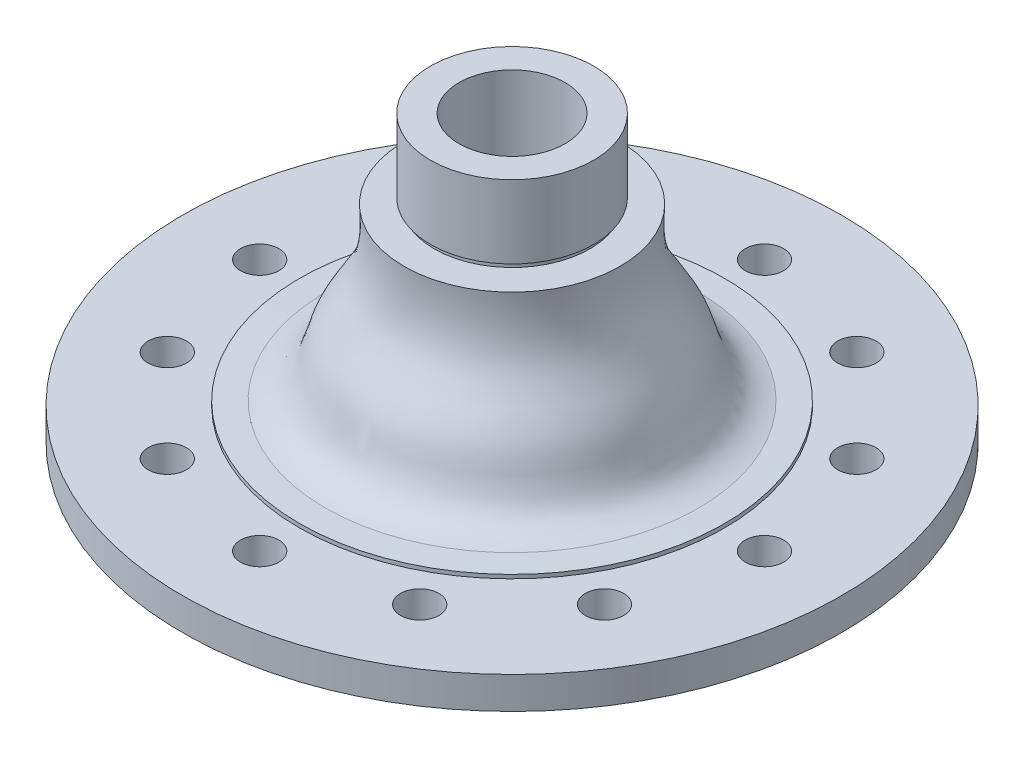
SolidWorks part; units mm, degrees
ref_plane "前视基准面" through (0, 0, 0) normal (0, 0, 1) x (1, 0, 0)
ref_plane "上视基准面" through (0, 0, 0) normal (0, 1, 0) x (1, 0, 0)
ref_plane "右视基准面" through (0, 0, 0) normal (1, 0, 0) x (0, 0, -1)
sketch "草图1" plane through (0, 0, 0) normal (0, 0, 1) x (1, 0, 0)
  line L0 (480.1019, -245.7954) -> (480.1019, -235.2999)
  line L1 (480.1019, -189.0989) -> (480.1019, -199.5944)
  line L2 (570.5144, -106.8394) -> (570.5144, -27.9384)
  line L3 (554.8914, -106.8394) -> (570.5144, -106.8394)
  line L4 (421.1305, -166.2628) -> (451.02, -166.2628)
  line L5 (538.9638, -278.2864) -> (554.8914, -278.2864)
  line L6 (538.9638, -156.6079) -> (554.8914, -156.6079)
  line L7 (479.0172, -166.2494) -> (436.8834, -166.2494)
  line L8 (417.9807, -168.3627) -> (417.9807, -180.6994)
  line L9 (417.9807, -266.5316) -> (417.9807, -254.1949)
  line L10 (479.0172, -164.221) -> (483.3535, -164.221)
  line L11 (554.8914, -156.6079) -> (554.8914, -106.8394)
  line L12 (554.8914, -67.8359) -> (554.8914, -43.8433)
  line L13 (628.5144, -106.8394) -> (628.5144, -27.9384)
  line L14 (644.1375, -106.8394) -> (628.5144, -106.8394)
  line L15 (660.0651, -156.6079) -> (644.1375, -156.6079)
  line L16 (644.1375, -156.6079) -> (644.1375, -106.8394)
  line L17 (660.0651, -278.2864) -> (644.1375, -278.2864)
  line L18 (644.1367, -27.9384) -> (644.1367, -67.8359)
  line L19 (554.8922, -27.9384) -> (554.8922, -66.786)
  line L20 (540.4804, -70.9857) -> (556.9913, -70.9857)
  line L21 (556.9913, -70.9857) -> (556.9913, -67.8359)
  line L22 (556.9913, -67.8359) -> (554.8914, -67.8359)
  line L23 (628.5144, -27.9384) -> (554.8922, -27.9384)
  line L24 (658.5485, -70.9857) -> (642.0376, -70.9857)
  line L25 (642.0376, -67.8359) -> (644.27, -67.8359)
  line L26 (642.0376, -70.9857) -> (642.0376, -67.8359)
  line L27 (644.1375, -328.0549) -> (628.5144, -328.0549)
  line L28 (554.8914, -67.8359) -> (554.7589, -67.8359)
  line L29 (715.6754, -164.221) -> (715.6754, -166.3209)
  line L30 (715.6754, -164.221) -> (701.5796, -163.8762)
  line L31 (483.3535, -164.221) -> (497.4492, -163.8762)
  line L32 (554.8914, -406.9559) -> (573.2661, -406.9559)
  line L33 (554.8914, -367.0584) -> (554.8914, -406.9559)
  line L34 (644.1367, -402.7562) -> (644.1367, -368.1083)
  line L35 (554.8922, -402.7562) -> (554.8922, -368.1083)
  line L36 (648.3364, -363.9086) -> (658.5485, -363.9086)
  line L37 (540.4804, -363.9086) -> (554.8914, -363.9086)
  line L38 (554.8914, -363.9086) -> (556.9913, -363.9086)
  line L39 (556.9913, -363.9086) -> (556.9913, -367.0584)
  line L40 (556.9913, -367.0584) -> (554.7589, -367.0584)
  line L41 (644.1367, -406.9559) -> (625.7628, -406.9559)
  line L42 (573.2661, -406.9559) -> (554.8914, -406.9559)
  line L43 (648.3364, -363.9086) -> (642.0376, -363.9086)
  line L44 (642.0376, -367.0584) -> (644.2621, -367.0584)
  line L45 (642.0376, -363.9086) -> (642.0376, -367.0584)
  line L46 (644.1375, -278.2864) -> (644.1375, -328.0549)
  line L47 (480.1019, -199.5944) -> (517.9771, -199.5944)
  line L48 (483.2517, -235.2999) -> (509.5902, -235.2999)
  line L49 (718.927, -199.5944) -> (681.1417, -199.5944)
  line L50 (718.927, -235.2999) -> (681.1417, -235.2999)
  line L51 (781.0482, -168.3627) -> (781.0482, -180.6994)
  line L52 (480.1019, -235.2999) -> (517.9758, -235.2999)
  line L53 (718.927, -199.5944) -> (681.053, -199.5944)
  line L54 (681.0398, -235.2999) -> (718.927, -235.2999)
  line L55 (718.927, -189.0989) -> (718.927, -199.5944)
  line L56 (718.927, -245.7954) -> (718.927, -235.2999)
  line L57 (660.0651, -156.6471) -> (660.0651, -156.6079)
  line L58 (456.4437, -166.2628) -> (420.0806, -166.2628)
  line L59 (479.0172, -164.221) -> (479.0172, -166.2494)
  line L60 (473.7676, -166.2494) -> (472.8541, -166.2494)
  line L61 (417.9807, -266.5316) -> (417.9807, -254.1949)
  line L62 (456.4437, -268.6315) -> (420.0806, -268.6315)
  line L63 (479.0172, -268.6315) -> (420.0806, -268.6315)
  line L64 (483.3535, -270.6733) -> (497.4492, -271.0181)
  line L65 (479.0172, -270.6733) -> (479.0172, -268.6315)
  line L66 (479.0172, -270.6733) -> (483.3535, -270.6733)
  line L67 (421.1305, -183.8492) -> (474.8522, -183.8492)
  line L68 (421.1305, -251.0451) -> (474.8522, -251.0451)
  line L69 (715.6754, -270.6733) -> (701.5796, -271.0181)
  line L70 (720.0116, -270.6733) -> (720.0116, -268.6315)
  line L71 (781.0482, -266.5316) -> (781.0482, -254.1949)
  line L72 (720.0116, -268.6315) -> (778.9483, -268.6315)
  line L73 (720.0116, -270.6733) -> (715.6754, -270.6733)
  line L74 (777.8983, -183.8492) -> (724.1766, -183.8492)
  line L75 (777.8983, -251.0451) -> (724.1766, -251.0451)
  line L76 (554.8914, -328.0549) -> (554.946, -328.0549)
  line L77 (554.946, -328.0549) -> (570.5144, -328.0549)
  line L78 (554.8914, -278.2864) -> (554.8914, -328.0549)
  line L79 (644.1367, -367.0584) -> (644.1367, -406.9559)
  line L80 (628.5144, -27.9384) -> (644.1367, -27.9384)
  line L81 (573.2661, -406.9559) -> (625.7628, -406.9559)
  line L82 (443.3195, -166.2494) -> (443.3195, -183.8492)
  line L83 (443.3195, -251.0451) -> (443.3195, -268.6315)
  line L84 (466.418, -166.2494) -> (466.418, -183.8492)
  line L85 (466.418, -251.0451) -> (466.418, -268.6315)
  line L86 (570.5144, -328.0549) -> (570.5144, -406.9559)
  line L87 (628.5144, -328.0549) -> (628.5144, -406.9559)
  line L88 (715.6754, -166.3209) -> (778.9483, -166.3209)
  line L89 (755.7094, -166.2494) -> (755.7094, -183.8492)
  line L90 (754.6595, -166.2494) -> (754.6595, -166.3209)
  line L91 (733.6608, -166.2494) -> (733.6608, -166.3209)
  line L92 (732.6108, -166.2494) -> (732.6108, -183.8492)
  line L93 (755.7094, -251.0451) -> (755.7094, -268.6315)
  line L94 (732.6108, -251.0451) -> (732.6108, -268.6315)
  arc A0 (525.3047, -175.8868) -> (517.9771, -199.5944) centre (584.1341, -207.0561) ccw
  arc A1 (417.9807, -180.6994) -> (421.1305, -183.8492) centre (421.1305, -180.6994) ccw
  arc A2 (420.0806, -166.2628) -> (417.9807, -168.3627) centre (420.0806, -168.3627) ccw
  arc A3 (421.1305, -251.0451) -> (417.9807, -254.1949) centre (421.1305, -254.1949) ccw
  arc A4 (681.053, -199.5944) -> (673.7242, -175.8868) centre (614.8603, -207.0702) ccw
  arc A5 (517.9758, -235.2999) -> (525.3047, -259.0076) centre (584.1686, -227.8242) ccw
  arc A6 (673.7242, -259.0076) -> (681.053, -235.2999) centre (614.8603, -227.8242) ccw
  arc A7 (781.0482, -168.3627) -> (778.9483, -166.2628) centre (778.9483, -168.3627) ccw
  arc A8 (777.8983, -183.8492) -> (781.0482, -180.6994) centre (777.8983, -180.6994) ccw
  arc A9 (480.1019, -189.0989) -> (474.8522, -183.8492) centre (474.8522, -189.0989) ccw
  arc A10 (474.8522, -251.0451) -> (480.1019, -245.7954) centre (474.8522, -245.7954) ccw
  arc A11 (724.1766, -183.8492) -> (718.927, -189.0989) centre (724.1766, -189.0989) ccw
  arc A12 (718.927, -245.7954) -> (724.1766, -251.0451) centre (724.1766, -245.7954) ccw
  arc A13 (417.9807, -266.5316) -> (420.0806, -268.6315) centre (420.0806, -266.5316) ccw
  arc A14 (421.1305, -251.0451) -> (417.9807, -254.1949) centre (421.1305, -254.1949) ccw
  arc A15 (781.0482, -254.1949) -> (777.8983, -251.0451) centre (777.8983, -254.1949) ccw
  arc A16 (778.9483, -268.6315) -> (781.0482, -266.5316) centre (778.9483, -266.5316) ccw
  spline S0 degree 3 poles (701.5796, -163.8762) (696.837, -162.8738) (682.4852, -157.6762) (679.9458, -129.4237) (658.4817, -105.8546) (657.727, -82.1258) (658.5485, -70.9857) knots 0 0 0 0 1057.430308 2997.111063 5402.743205 7834.148235 7834.148235 7834.148235 7834.148235 weights 1 1 1 1 1 1 1
  spline S1 degree 3 poles (497.4492, -163.8762) (502.1919, -162.8738) (516.5437, -157.6762) (519.083, -129.4237) (540.5472, -105.8546) (541.3019, -82.1258) (540.4804, -70.9857) knots 0 0 0 0 836.310079 2370.382399 4272.970581 6195.942259 6195.942259 6195.942259 6195.942259 weights 1 1 1 1 1 1 1
  spline S2 degree 3 poles (538.9638, -156.6079) (535.9309, -156.9888) (531.5182, -158.6747) (524.9801, -164.8379) (524.3832, -171.6216) (525.3047, -175.8868) knots 0 0 0 0 1737.139201 2548.792041 5028.650795 5028.650795 5028.650795 5028.650795 weights 1 1 1 1 1 1
  spline S3 degree 3 poles (660.0651, -156.6079) (663.098, -156.9888) (667.5107, -158.6747) (674.0488, -164.8379) (674.6457, -171.6216) (673.7242, -175.8868) knots 0 0 0 0 2126.07148 3119.447228 6154.52753 6154.52753 6154.52753 6154.52753 weights 1 1 1 1 1 1
  spline S4 degree 3 poles (538.9638, -278.2864) (535.9309, -277.9055) (531.5182, -276.2196) (524.9801, -270.0564) (524.3832, -263.2727) (525.3047, -259.0076) knots 0 0 0 0 1950.629452 2862.032483 5646.659944 5646.659944 5646.659944 5646.659944 weights 1 1 1 1 1 1
  spline S5 degree 3 poles (660.0651, -278.2864) (663.098, -277.9055) (667.5107, -276.2196) (674.0488, -270.0564) (674.6457, -263.2727) (673.7242, -259.0076) knots 0 0 0 0 2328.664854 3416.699389 6740.992526 6740.992526 6740.992526 6740.992526 weights 1 1 1 1 1 1
  spline S6 degree 3 poles (497.4492, -271.0181) (502.1919, -272.0205) (516.5437, -277.2181) (519.083, -305.4706) (540.5472, -329.0397) (541.3019, -352.7686) (540.4804, -363.9086) knots 0 0 0 0 1000.918373 2836.937343 5114.005999 7415.470169 7415.470169 7415.470169 7415.470169 weights 1 1 1 1 1 1 1
  spline S7 degree 3 poles (701.5796, -271.0181) (696.837, -272.0205) (682.4852, -277.2181) (679.9458, -305.4706) (658.4817, -329.0397) (657.727, -352.7686) (658.5485, -363.9086) knots 0 0 0 0 1212.145887 3435.626744 6193.233637 8980.38432 8980.38432 8980.38432 8980.38432 weights 1 1 1 1 1 1 1
  dimension "D1" = 58
sketch "草图2" plane through (0, 0, 0) normal (0, 0, 1) x (1, 0, 0)
  line L0 (628.5144, -67.3889) -> (570.5144, -67.3889)
  line L1 (628.5144, -106.8394) -> (628.5144, -27.9384) construction
  line L2 (570.5144, -106.8394) -> (570.5144, -27.9384) construction
  line L3 (599.5144, -67.3889) -> (599.5144, -145.6422)
  line L4 (628.5144, -106.8394) -> (628.5144, -27.9384)
  line L5 (658.5485, -70.9857) -> (642.0376, -70.9857) construction
  line L6 (658.5485, -70.9857) -> (642.0376, -70.9857)
  line L7 (421.1305, -166.2628) -> (451.02, -166.2628) construction
  line L8 (554.8914, -106.8394) -> (570.5144, -106.8394) construction
  line L9 (554.8914, -156.6079) -> (554.8914, -106.8394) construction
  line L10 (538.9638, -156.6079) -> (554.8914, -156.6079) construction
  line L11 (570.5144, -328.0549) -> (570.5144, -406.9559) construction
  line L12 (554.946, -328.0549) -> (570.5144, -328.0549) construction
  line L13 (554.8914, -328.0549) -> (554.946, -328.0549) construction
  line L14 (554.8914, -278.2864) -> (554.8914, -328.0549) construction
  line L15 (538.9638, -278.2864) -> (554.8914, -278.2864) construction
  line L16 (480.1019, -235.2999) -> (517.9758, -235.2999) construction
  line L17 (480.1019, -245.7954) -> (480.1019, -235.2999) construction
  line L18 (421.1305, -251.0451) -> (474.8522, -251.0451) construction
  line L19 (417.9807, -266.5316) -> (417.9807, -254.1949) construction
  line L20 (417.9807, -266.5316) -> (417.9807, -254.1949) construction
  line L21 (556.9913, -67.8359) -> (554.8914, -67.8359) construction
  line L22 (556.9913, -70.9857) -> (556.9913, -67.8359) construction
  line L23 (540.4804, -70.9857) -> (556.9913, -70.9857) construction
  line L24 (483.3535, -164.221) -> (497.4492, -163.8762) construction
  line L25 (479.0172, -164.221) -> (483.3535, -164.221) construction
  line L26 (479.0172, -164.221) -> (479.0172, -166.2494) construction
  line L27 (479.0172, -166.2494) -> (436.8834, -166.2494) construction
  line L28 (644.1367, -27.9384) -> (644.1367, -67.8359) construction
  line L29 (628.5144, -27.9384) -> (644.1367, -27.9384) construction
  line L30 (644.1375, -106.8394) -> (628.5144, -106.8394) construction
  line L31 (644.1375, -156.6079) -> (644.1375, -106.8394) construction
  line L32 (660.0651, -156.6079) -> (644.1375, -156.6079) construction
  line L33 (660.0651, -156.6471) -> (660.0651, -156.6079) construction
  line L34 (718.927, -199.5944) -> (681.053, -199.5944) construction
  line L35 (554.8922, -27.9384) -> (554.8922, -66.786) construction
  line L36 (628.5144, -27.9384) -> (554.8922, -27.9384) construction
  line L37 (554.8914, -67.8359) -> (554.8914, -43.8433) construction
  line L38 (554.8914, -67.8359) -> (554.7589, -67.8359) construction
  line L39 (554.8914, -406.9559) -> (573.2661, -406.9559) construction
  line L40 (554.8914, -367.0584) -> (554.8914, -406.9559) construction
  line L41 (573.2661, -406.9559) -> (554.8914, -406.9559) construction
  line L42 (642.0376, -67.8359) -> (644.27, -67.8359) construction
  line L43 (642.0376, -70.9857) -> (642.0376, -67.8359) construction
  line L44 (715.6754, -164.221) -> (701.5796, -163.8762) construction
  line L45 (715.6754, -164.221) -> (715.6754, -166.3209) construction
  line L46 (715.6754, -166.3209) -> (778.9483, -166.3209) construction
  line L47 (479.0172, -268.6315) -> (420.0806, -268.6315) construction
  line L48 (479.0172, -270.6733) -> (479.0172, -268.6315) construction
  line L49 (479.0172, -270.6733) -> (483.3535, -270.6733) construction
  line L50 (483.3535, -270.6733) -> (497.4492, -271.0181) construction
  line L51 (540.4804, -363.9086) -> (554.8914, -363.9086) construction
  line L52 (554.8914, -363.9086) -> (556.9913, -363.9086) construction
  line L53 (556.9913, -363.9086) -> (556.9913, -367.0584) construction
  line L54 (556.9913, -367.0584) -> (554.7589, -367.0584) construction
  line L55 (554.8922, -402.7562) -> (554.8922, -368.1083) construction
  line L56 (644.1367, -402.7562) -> (644.1367, -368.1083) construction
  line L57 (573.2661, -406.9559) -> (625.7628, -406.9559) construction
  line L58 (644.1367, -406.9559) -> (625.7628, -406.9559) construction
  line L59 (644.1367, -367.0584) -> (644.1367, -406.9559) construction
  line L60 (660.0651, -278.2864) -> (644.1375, -278.2864) construction
  line L61 (644.1375, -278.2864) -> (644.1375, -328.0549) construction
  line L62 (644.1375, -328.0549) -> (628.5144, -328.0549) construction
  line L63 (628.5144, -328.0549) -> (628.5144, -406.9559) construction
  line L64 (718.927, -235.2999) -> (681.1417, -235.2999) construction
  line L65 (681.0398, -235.2999) -> (718.927, -235.2999) construction
  line L66 (642.0376, -367.0584) -> (644.2621, -367.0584) construction
  line L67 (642.0376, -363.9086) -> (642.0376, -367.0584) construction
  line L68 (648.3364, -363.9086) -> (642.0376, -363.9086) construction
  line L69 (648.3364, -363.9086) -> (658.5485, -363.9086) construction
  line L70 (715.6754, -270.6733) -> (701.5796, -271.0181) construction
  line L71 (720.0116, -270.6733) -> (715.6754, -270.6733) construction
  line L72 (720.0116, -270.6733) -> (720.0116, -268.6315) construction
  line L73 (720.0116, -268.6315) -> (778.9483, -268.6315) construction
  line L74 (781.0482, -266.5316) -> (781.0482, -254.1949) construction
  line L75 (777.8983, -251.0451) -> (724.1766, -251.0451) construction
  line L76 (718.927, -245.7954) -> (718.927, -235.2999) construction
  line L77 (718.927, -199.5944) -> (681.1417, -199.5944) construction
  line L78 (781.0482, -168.3627) -> (781.0482, -180.6994) construction
  line L79 (777.8983, -183.8492) -> (724.1766, -183.8492) construction
  line L80 (718.927, -189.0989) -> (718.927, -199.5944) construction
  line L81 (483.2517, -235.2999) -> (509.5902, -235.2999) construction
  line L82 (456.4437, -166.2628) -> (420.0806, -166.2628) construction
  line L83 (417.9807, -168.3627) -> (417.9807, -180.6994) construction
  line L84 (421.1305, -183.8492) -> (474.8522, -183.8492) construction
  line L85 (480.1019, -189.0989) -> (480.1019, -199.5944) construction
  line L86 (480.1019, -199.5944) -> (517.9771, -199.5944) construction
  line L87 (456.4437, -268.6315) -> (420.0806, -268.6315) construction
  line L88 (473.7676, -166.2494) -> (472.8541, -166.2494) construction
  line L89 (466.418, -251.0451) -> (466.418, -268.6315) construction
  line L90 (466.418, -166.2494) -> (466.418, -183.8492) construction
  line L91 (443.3195, -251.0451) -> (443.3195, -268.6315) construction
  line L92 (443.3195, -166.2494) -> (443.3195, -183.8492) construction
  line L93 (732.6108, -251.0451) -> (732.6108, -268.6315) construction
  line L94 (755.7094, -251.0451) -> (755.7094, -268.6315) construction
  line L95 (732.6108, -166.2494) -> (732.6108, -183.8492) construction
  line L96 (733.6608, -166.2494) -> (733.6608, -166.3209) construction
  line L97 (754.6595, -166.2494) -> (754.6595, -166.3209) construction
  line L98 (755.7094, -166.2494) -> (755.7094, -183.8492) construction
  line L99 (421.1305, -166.2628) -> (451.02, -166.2628)
  line L100 (570.5144, -106.8394) -> (570.5144, -27.9384)
  line L101 (554.8914, -106.8394) -> (570.5144, -106.8394)
  line L102 (554.8914, -156.6079) -> (554.8914, -106.8394)
  line L103 (538.9638, -156.6079) -> (554.8914, -156.6079)
  line L104 (570.5144, -328.0549) -> (570.5144, -406.9559)
  line L105 (554.946, -328.0549) -> (570.5144, -328.0549)
  line L106 (554.8914, -328.0549) -> (554.946, -328.0549)
  line L107 (554.8914, -278.2864) -> (554.8914, -328.0549)
  line L108 (538.9638, -278.2864) -> (554.8914, -278.2864)
  line L109 (480.1019, -235.2999) -> (517.9758, -235.2999)
  line L110 (480.1019, -245.7954) -> (480.1019, -235.2999)
  line L111 (421.1305, -251.0451) -> (474.8522, -251.0451)
  line L112 (417.9807, -266.5316) -> (417.9807, -254.1949)
  line L113 (417.9807, -266.5316) -> (417.9807, -254.1949)
  line L114 (556.9913, -67.8359) -> (554.8914, -67.8359)
  line L115 (556.9913, -70.9857) -> (556.9913, -67.8359)
  line L116 (540.4804, -70.9857) -> (556.9913, -70.9857)
  line L117 (483.3535, -164.221) -> (497.4492, -163.8762)
  line L118 (479.0172, -164.221) -> (483.3535, -164.221)
  line L119 (479.0172, -164.221) -> (479.0172, -166.2494)
  line L120 (479.0172, -166.2494) -> (436.8834, -166.2494)
  line L121 (644.1367, -27.9384) -> (644.1367, -67.8359)
  line L122 (628.5144, -27.9384) -> (644.1367, -27.9384)
  line L123 (628.5144, -106.8394) -> (628.5144, -27.9384)
  line L124 (644.1375, -106.8394) -> (628.5144, -106.8394)
  line L125 (644.1375, -156.6079) -> (644.1375, -106.8394)
  line L126 (660.0651, -156.6079) -> (644.1375, -156.6079)
  line L127 (660.0651, -156.6471) -> (660.0651, -156.6079)
  line L128 (718.927, -199.5944) -> (681.053, -199.5944)
  line L129 (554.8922, -27.9384) -> (554.8922, -66.786)
  line L130 (628.5144, -27.9384) -> (554.8922, -27.9384)
  line L131 (554.8914, -67.8359) -> (554.8914, -43.8433)
  line L132 (554.8914, -67.8359) -> (554.7589, -67.8359)
  line L133 (554.8914, -406.9559) -> (573.2661, -406.9559)
  line L134 (554.8914, -367.0584) -> (554.8914, -406.9559)
  line L135 (573.2661, -406.9559) -> (554.8914, -406.9559)
  line L136 (642.0376, -67.8359) -> (644.27, -67.8359)
  line L137 (642.0376, -70.9857) -> (642.0376, -67.8359)
  line L138 (658.5485, -70.9857) -> (642.0376, -70.9857)
  line L139 (715.6754, -164.221) -> (701.5796, -163.8762)
  line L140 (715.6754, -164.221) -> (715.6754, -166.3209)
  line L141 (715.6754, -166.3209) -> (778.9483, -166.3209)
  line L142 (479.0172, -268.6315) -> (420.0806, -268.6315)
  line L143 (479.0172, -270.6733) -> (479.0172, -268.6315)
  line L144 (479.0172, -270.6733) -> (483.3535, -270.6733)
  line L145 (483.3535, -270.6733) -> (497.4492, -271.0181)
  line L146 (540.4804, -363.9086) -> (554.8914, -363.9086)
  line L147 (554.8914, -363.9086) -> (556.9913, -363.9086)
  line L148 (556.9913, -363.9086) -> (556.9913, -367.0584)
  line L149 (556.9913, -367.0584) -> (554.7589, -367.0584)
  line L150 (554.8922, -402.7562) -> (554.8922, -368.1083)
  line L151 (644.1367, -402.7562) -> (644.1367, -368.1083)
  line L152 (573.2661, -406.9559) -> (625.7628, -406.9559)
  line L153 (644.1367, -406.9559) -> (625.7628, -406.9559)
  line L154 (644.1367, -367.0584) -> (644.1367, -406.9559)
  line L155 (660.0651, -278.2864) -> (644.1375, -278.2864)
  line L156 (644.1375, -278.2864) -> (644.1375, -328.0549)
  line L157 (644.1375, -328.0549) -> (628.5144, -328.0549)
  line L158 (628.5144, -328.0549) -> (628.5144, -406.9559)
  line L159 (718.927, -235.2999) -> (681.1417, -235.2999)
  line L160 (681.0398, -235.2999) -> (718.927, -235.2999)
  line L161 (642.0376, -367.0584) -> (644.2621, -367.0584)
  line L162 (642.0376, -363.9086) -> (642.0376, -367.0584)
  line L163 (648.3364, -363.9086) -> (642.0376, -363.9086)
  line L164 (648.3364, -363.9086) -> (658.5485, -363.9086)
  line L165 (715.6754, -270.6733) -> (701.5796, -271.0181)
  line L166 (720.0116, -270.6733) -> (715.6754, -270.6733)
  line L167 (720.0116, -270.6733) -> (720.0116, -268.6315)
  line L168 (720.0116, -268.6315) -> (778.9483, -268.6315)
  line L169 (781.0482, -266.5316) -> (781.0482, -254.1949)
  line L170 (777.8983, -251.0451) -> (724.1766, -251.0451)
  line L171 (718.927, -245.7954) -> (718.927, -235.2999)
  line L172 (718.927, -199.5944) -> (681.1417, -199.5944)
  line L173 (781.0482, -168.3627) -> (781.0482, -180.6994)
  line L174 (777.8983, -183.8492) -> (724.1766, -183.8492)
  line L175 (718.927, -189.0989) -> (718.927, -199.5944)
  line L176 (483.2517, -235.2999) -> (509.5902, -235.2999)
  line L177 (456.4437, -166.2628) -> (420.0806, -166.2628)
  line L178 (417.9807, -168.3627) -> (417.9807, -180.6994)
  line L179 (421.1305, -183.8492) -> (474.8522, -183.8492)
  line L180 (480.1019, -189.0989) -> (480.1019, -199.5944)
  line L181 (480.1019, -199.5944) -> (517.9771, -199.5944)
  line L182 (456.4437, -268.6315) -> (420.0806, -268.6315)
  line L183 (473.7676, -166.2494) -> (472.8541, -166.2494)
  line L184 (466.418, -251.0451) -> (466.418, -268.6315)
  line L185 (466.418, -166.2494) -> (466.418, -183.8492)
  line L186 (443.3195, -251.0451) -> (443.3195, -268.6315)
  line L187 (443.3195, -166.2494) -> (443.3195, -183.8492)
  line L188 (732.6108, -251.0451) -> (732.6108, -268.6315)
  line L189 (755.7094, -251.0451) -> (755.7094, -268.6315)
  line L190 (732.6108, -166.2494) -> (732.6108, -183.8492)
  line L191 (733.6608, -166.2494) -> (733.6608, -166.3209)
  line L193 (755.7094, -166.2494) -> (755.7094, -183.8492)
  line L194 (421.1305, -166.2628) -> (451.02, -166.2628)
  line L195 (570.5144, -106.8394) -> (570.5144, -27.9384)
  line L196 (554.8914, -106.8394) -> (570.5144, -106.8394)
  line L197 (554.8914, -156.6079) -> (554.8914, -106.8394)
  line L198 (538.9638, -156.6079) -> (554.8914, -156.6079)
  line L199 (570.5144, -328.0549) -> (570.5144, -406.9559)
  line L200 (554.946, -328.0549) -> (570.5144, -328.0549)
  line L201 (554.8914, -328.0549) -> (554.946, -328.0549)
  line L202 (554.8914, -278.2864) -> (554.8914, -328.0549)
  line L203 (538.9638, -278.2864) -> (554.8914, -278.2864)
  line L204 (480.1019, -235.2999) -> (517.9758, -235.2999)
  line L205 (480.1019, -245.7954) -> (480.1019, -235.2999)
  line L206 (421.1305, -251.0451) -> (474.8522, -251.0451)
  line L207 (417.9807, -266.5316) -> (417.9807, -254.1949)
  line L208 (417.9807, -266.5316) -> (417.9807, -254.1949)
  line L209 (556.9913, -67.8359) -> (554.8914, -67.8359)
  line L210 (556.9913, -70.9857) -> (556.9913, -67.8359)
  line L211 (540.4804, -70.9857) -> (556.9913, -70.9857)
  line L212 (483.3535, -164.221) -> (497.4492, -163.8762)
  line L213 (479.0172, -164.221) -> (483.3535, -164.221)
  line L214 (479.0172, -164.221) -> (479.0172, -166.2494)
  line L215 (479.0172, -166.2494) -> (436.8834, -166.2494)
  line L216 (644.1367, -27.9384) -> (644.1367, -67.8359)
  line L217 (628.5144, -27.9384) -> (644.1367, -27.9384)
  line L218 (628.5144, -106.8394) -> (628.5144, -27.9384)
  line L219 (644.1375, -106.8394) -> (628.5144, -106.8394)
  line L220 (644.1375, -156.6079) -> (644.1375, -106.8394)
  line L221 (660.0651, -156.6079) -> (644.1375, -156.6079)
  line L222 (660.0651, -156.6471) -> (660.0651, -156.6079)
  line L223 (718.927, -199.5944) -> (681.053, -199.5944)
  line L224 (554.8922, -27.9384) -> (554.8922, -66.786)
  line L225 (628.5144, -27.9384) -> (554.8922, -27.9384)
  line L226 (554.8914, -67.8359) -> (554.8914, -43.8433)
  line L227 (554.8914, -67.8359) -> (554.7589, -67.8359)
  line L228 (554.8914, -406.9559) -> (573.2661, -406.9559)
  line L229 (554.8914, -367.0584) -> (554.8914, -406.9559)
  line L230 (573.2661, -406.9559) -> (554.8914, -406.9559)
  line L231 (642.0376, -67.8359) -> (644.27, -67.8359)
  line L232 (642.0376, -70.9857) -> (642.0376, -67.8359)
  line L233 (658.5485, -70.9857) -> (642.0376, -70.9857)
  line L234 (715.6754, -164.221) -> (701.5796, -163.8762)
  line L235 (715.6754, -164.221) -> (715.6754, -166.3209)
  line L236 (715.6754, -166.3209) -> (778.9483, -166.3209)
  line L237 (479.0172, -268.6315) -> (420.0806, -268.6315)
  line L238 (479.0172, -270.6733) -> (479.0172, -268.6315)
  line L239 (479.0172, -270.6733) -> (483.3535, -270.6733)
  line L240 (483.3535, -270.6733) -> (497.4492, -271.0181)
  line L241 (540.4804, -363.9086) -> (554.8914, -363.9086)
  line L242 (554.8914, -363.9086) -> (556.9913, -363.9086)
  line L243 (556.9913, -363.9086) -> (556.9913, -367.0584)
  line L244 (556.9913, -367.0584) -> (554.7589, -367.0584)
  line L245 (554.8922, -402.7562) -> (554.8922, -368.1083)
  line L246 (644.1367, -402.7562) -> (644.1367, -368.1083)
  line L247 (573.2661, -406.9559) -> (625.7628, -406.9559)
  line L248 (644.1367, -406.9559) -> (625.7628, -406.9559)
  line L249 (644.1367, -367.0584) -> (644.1367, -406.9559)
  line L250 (660.0651, -278.2864) -> (644.1375, -278.2864)
  line L251 (644.1375, -278.2864) -> (644.1375, -328.0549)
  line L252 (644.1375, -328.0549) -> (628.5144, -328.0549)
  line L253 (628.5144, -328.0549) -> (628.5144, -406.9559)
  line L254 (718.927, -235.2999) -> (681.1417, -235.2999)
  line L255 (681.0398, -235.2999) -> (718.927, -235.2999)
  line L256 (642.0376, -367.0584) -> (644.2621, -367.0584)
  line L257 (642.0376, -363.9086) -> (642.0376, -367.0584)
  line L258 (648.3364, -363.9086) -> (642.0376, -363.9086)
  line L259 (648.3364, -363.9086) -> (658.5485, -363.9086)
  line L260 (715.6754, -270.6733) -> (701.5796, -271.0181)
  line L261 (720.0116, -270.6733) -> (715.6754, -270.6733)
  line L262 (720.0116, -270.6733) -> (720.0116, -268.6315)
  line L263 (720.0116, -268.6315) -> (778.9483, -268.6315)
  line L264 (781.0482, -266.5316) -> (781.0482, -254.1949)
  line L265 (777.8983, -251.0451) -> (724.1766, -251.0451)
  line L266 (718.927, -245.7954) -> (718.927, -235.2999)
  line L267 (718.927, -199.5944) -> (681.1417, -199.5944)
  line L268 (781.0482, -168.3627) -> (781.0482, -180.6994)
  line L269 (777.8983, -183.8492) -> (724.1766, -183.8492)
  line L270 (718.927, -189.0989) -> (718.927, -199.5944)
  line L271 (483.2517, -235.2999) -> (509.5902, -235.2999)
  line L272 (456.4437, -166.2628) -> (420.0806, -166.2628)
  line L273 (417.9807, -168.3627) -> (417.9807, -180.6994)
  line L274 (421.1305, -183.8492) -> (474.8522, -183.8492)
  line L275 (480.1019, -189.0989) -> (480.1019, -199.5944)
  line L276 (480.1019, -199.5944) -> (517.9771, -199.5944)
  line L277 (456.4437, -268.6315) -> (420.0806, -268.6315)
  line L278 (473.7676, -166.2494) -> (472.8541, -166.2494)
  line L279 (466.418, -251.0451) -> (466.418, -268.6315)
  line L280 (466.418, -166.2494) -> (466.418, -183.8492)
  line L281 (443.3195, -251.0451) -> (443.3195, -268.6315)
  line L282 (443.3195, -166.2494) -> (443.3195, -183.8492)
  line L283 (732.6108, -251.0451) -> (732.6108, -268.6315)
  line L284 (755.7094, -251.0451) -> (755.7094, -268.6315)
  line L285 (732.6108, -166.2494) -> (732.6108, -183.8492)
  line L286 (733.6608, -166.2494) -> (733.6608, -166.3209)
  line L287 (754.6595, -166.2494) -> (754.6595, -166.3209)
  line L288 (755.7094, -166.2494) -> (755.7094, -183.8492)
  arc A0 (525.3047, -175.8868) -> (517.9771, -199.5944) centre (584.1341, -207.0561) ccw construction
  arc A1 (517.9758, -235.2999) -> (525.3047, -259.0076) centre (584.1686, -227.8242) ccw construction
  arc A2 (474.8522, -251.0451) -> (480.1019, -245.7954) centre (474.8522, -245.7954) ccw construction
  arc A3 (421.1305, -251.0451) -> (417.9807, -254.1949) centre (421.1305, -254.1949) ccw construction
  arc A4 (421.1305, -251.0451) -> (417.9807, -254.1949) centre (421.1305, -254.1949) ccw construction
  arc A5 (417.9807, -266.5316) -> (420.0806, -268.6315) centre (420.0806, -266.5316) ccw construction
  arc A6 (681.053, -199.5944) -> (673.7242, -175.8868) centre (614.8603, -207.0702) ccw construction
  arc A7 (673.7242, -259.0076) -> (681.053, -235.2999) centre (614.8603, -227.8242) ccw construction
  arc A8 (778.9483, -268.6315) -> (781.0482, -266.5316) centre (778.9483, -266.5316) ccw construction
  arc A9 (781.0482, -254.1949) -> (777.8983, -251.0451) centre (777.8983, -254.1949) ccw construction
  arc A10 (718.927, -245.7954) -> (724.1766, -251.0451) centre (724.1766, -245.7954) ccw construction
  arc A11 (781.0482, -168.3627) -> (778.9483, -166.2628) centre (778.9483, -168.3627) ccw construction
  arc A12 (777.8983, -183.8492) -> (781.0482, -180.6994) centre (777.8983, -180.6994) ccw construction
  arc A13 (724.1766, -183.8492) -> (718.927, -189.0989) centre (724.1766, -189.0989) ccw construction
  arc A14 (420.0806, -166.2628) -> (417.9807, -168.3627) centre (420.0806, -168.3627) ccw construction
  arc A15 (417.9807, -180.6994) -> (421.1305, -183.8492) centre (421.1305, -180.6994) ccw construction
  arc A16 (480.1019, -189.0989) -> (474.8522, -183.8492) centre (474.8522, -189.0989) ccw construction
  arc A17 (525.3047, -175.8868) -> (517.9771, -199.5944) centre (584.1341, -207.0561) ccw
  arc A18 (517.9758, -235.2999) -> (525.3047, -259.0076) centre (584.1686, -227.8242) ccw
  arc A19 (474.8522, -251.0451) -> (480.1019, -245.7954) centre (474.8522, -245.7954) ccw
  arc A20 (421.1305, -251.0451) -> (417.9807, -254.1949) centre (421.1305, -254.1949) ccw
  arc A21 (421.1305, -251.0451) -> (417.9807, -254.1949) centre (421.1305, -254.1949) ccw
  arc A22 (417.9807, -266.5316) -> (420.0806, -268.6315) centre (420.0806, -266.5316) ccw
  arc A23 (681.053, -199.5944) -> (673.7242, -175.8868) centre (614.8603, -207.0702) ccw
  arc A24 (673.7242, -259.0076) -> (681.053, -235.2999) centre (614.8603, -227.8242) ccw
  arc A25 (778.9483, -268.6315) -> (781.0482, -266.5316) centre (778.9483, -266.5316) ccw
  arc A26 (781.0482, -254.1949) -> (777.8983, -251.0451) centre (777.8983, -254.1949) ccw
  arc A27 (718.927, -245.7954) -> (724.1766, -251.0451) centre (724.1766, -245.7954) ccw
  arc A28 (781.0482, -168.3627) -> (778.9483, -166.2628) centre (778.9483, -168.3627) ccw
  arc A29 (777.8983, -183.8492) -> (781.0482, -180.6994) centre (777.8983, -180.6994) ccw
  arc A30 (724.1766, -183.8492) -> (718.927, -189.0989) centre (724.1766, -189.0989) ccw
  arc A31 (420.0806, -166.2628) -> (417.9807, -168.3627) centre (420.0806, -168.3627) ccw
  arc A32 (417.9807, -180.6994) -> (421.1305, -183.8492) centre (421.1305, -180.6994) ccw
  arc A33 (480.1019, -189.0989) -> (474.8522, -183.8492) centre (474.8522, -189.0989) ccw
  arc A34 (525.3047, -175.8868) -> (517.9771, -199.5944) centre (584.1341, -207.0561) ccw
  arc A35 (517.9758, -235.2999) -> (525.3047, -259.0076) centre (584.1686, -227.8242) ccw
  arc A36 (474.8522, -251.0451) -> (480.1019, -245.7954) centre (474.8522, -245.7954) ccw
  arc A37 (421.1305, -251.0451) -> (417.9807, -254.1949) centre (421.1305, -254.1949) ccw
  arc A38 (421.1305, -251.0451) -> (417.9807, -254.1949) centre (421.1305, -254.1949) ccw
  arc A39 (417.9807, -266.5316) -> (420.0806, -268.6315) centre (420.0806, -266.5316) ccw
  arc A40 (681.053, -199.5944) -> (673.7242, -175.8868) centre (614.8603, -207.0702) ccw
  arc A41 (673.7242, -259.0076) -> (681.053, -235.2999) centre (614.8603, -227.8242) ccw
  arc A42 (778.9483, -268.6315) -> (781.0482, -266.5316) centre (778.9483, -266.5316) ccw
  arc A43 (781.0482, -254.1949) -> (777.8983, -251.0451) centre (777.8983, -254.1949) ccw
  arc A44 (718.927, -245.7954) -> (724.1766, -251.0451) centre (724.1766, -245.7954) ccw
  arc A45 (781.0482, -168.3627) -> (778.9483, -166.2628) centre (778.9483, -168.3627) ccw
  arc A46 (777.8983, -183.8492) -> (781.0482, -180.6994) centre (777.8983, -180.6994) ccw
  arc A47 (724.1766, -183.8492) -> (718.927, -189.0989) centre (724.1766, -189.0989) ccw
  arc A48 (420.0806, -166.2628) -> (417.9807, -168.3627) centre (420.0806, -168.3627) ccw
  arc A49 (417.9807, -180.6994) -> (421.1305, -183.8492) centre (421.1305, -180.6994) ccw
  arc A50 (480.1019, -189.0989) -> (474.8522, -183.8492) centre (474.8522, -189.0989) ccw
  spline S0 degree 3 poles (-4013.812, -2179.6252) (899.6159, -414.8523) (579.95, -113.02) (484.6705, -202.8362) (839.861, -543.3557) (-202.3937, 4763.1492) knots -37250.296744 -37250.296744 -37250.296744 -37250.296744 1737.139201 2548.792041 36031.94725 36031.94725 36031.94725 36031.94725 weights 1 1 1 1 1 1 only from (538.9638, -156.6079) to (525.3047, -175.8868) construction
  spline S1 degree 3 poles (-4013.812, 1744.7309) (899.6159, -20.042) (579.95, -321.8743) (484.6705, -232.0581) (839.861, 108.4614) (-202.3937, -5198.0435) knots -41828.269069 -41828.269069 -41828.269069 -41828.269069 1950.629452 2862.032483 40460.187337 40460.187337 40460.187337 40460.187337 weights 1 1 1 1 1 1 only from (538.9638, -278.2864) to (525.3047, -259.0076) construction
  spline S2 degree 3 poles (5433.8284, -948.6559) (61.9085, 31.1101) (509.7425, -233.3446) (519.083, -129.4237) (629.1326, -8.5817) (63.0507, 423.1658) (3809.232, -3853.8505) knots -11444.280389 -11444.280389 -11444.280389 -11444.280389 836.310079 2370.382399 4272.970581 28315.859287 28315.859287 28315.859287 28315.859287 weights 1 1 1 1 1 1 1 only from (497.4492, -163.8762) to (540.4804, -70.9857) construction
  spline S3 degree 3 poles (5212.8408, -2179.6252) (299.413, -414.8523) (619.0788, -113.02) (714.3584, -202.8362) (359.1679, -543.3557) (1401.4226, 4763.1492) knots -45590.355375 -45590.355375 -45590.355375 -45590.355375 2126.07148 3119.447228 44099.226679 44099.226679 44099.226679 44099.226679 weights 1 1 1 1 1 1 only from (660.0651, -156.6079) to (673.7242, -175.8868) construction
  spline S4 degree 3 poles (-4234.7995, -948.6559) (1137.1203, 31.1101) (689.2864, -233.3446) (679.9458, -129.4237) (569.8963, -8.5817) (1135.9782, 423.1658) (-2610.2031, -3853.8505) knots -14470.145986 -14470.145986 -14470.145986 -14470.145986 1057.430308 2997.111063 5402.743205 35802.567192 35802.567192 35802.567192 35802.567192 weights 1 1 1 1 1 1 1 only from (701.5796, -163.8762) to (658.5485, -70.9857) construction
  spline S5 degree 3 poles (5433.8284, 513.7616) (61.9085, -466.0044) (509.7425, -201.5498) (519.083, -305.4706) (629.1326, -426.3126) (63.0507, -858.0602) (3809.232, 3418.9562) knots -13696.822256 -13696.822256 -13696.822256 -13696.822256 1000.918373 2836.937343 5114.005999 33889.181189 33889.181189 33889.181189 33889.181189 weights 1 1 1 1 1 1 1 only from (497.4492, -271.0181) to (540.4804, -363.9086) construction
  spline S6 degree 3 poles (5212.8408, 1744.7309) (299.413, -20.042) (619.0788, -321.8743) (714.3584, -232.0581) (359.1679, 108.4614) (1401.4226, -5198.0435) knots -49934.660844 -49934.660844 -49934.660844 -49934.660844 2328.664854 3416.699389 48301.442478 48301.442478 48301.442478 48301.442478 weights 1 1 1 1 1 1 only from (660.0651, -278.2864) to (673.7242, -259.0076) construction
  spline S7 degree 3 poles (-4234.7995, 513.7616) (1137.1203, -466.0044) (689.2864, -201.5498) (679.9458, -305.4706) (569.8963, -426.3126) (1135.9782, -858.0602) (-2610.2031, 3418.9562) knots -16587.313416 -16587.313416 -16587.313416 -16587.313416 1212.145887 3435.626744 6193.233637 41040.940686 41040.940686 41040.940686 41040.940686 weights 1 1 1 1 1 1 1 only from (701.5796, -271.0181) to (658.5485, -363.9086) construction
  spline S8 degree 3 poles (538.9638, -156.6079) (535.9309, -156.9888) (531.5182, -158.6747) (524.9801, -164.8379) (524.3832, -171.6216) (525.3047, -175.8868) knots 0 0 0 0 1737.139201 2548.792041 5028.650795 5028.650795 5028.650795 5028.650795 weights 1 1 1 1 1 1
  spline S9 degree 3 poles (538.9638, -278.2864) (535.9309, -277.9055) (531.5182, -276.2196) (524.9801, -270.0564) (524.3832, -263.2727) (525.3047, -259.0076) knots 0 0 0 0 1950.629452 2862.032483 5646.659944 5646.659944 5646.659944 5646.659944 weights 1 1 1 1 1 1
  spline S10 degree 3 poles (497.4492, -163.8762) (502.1919, -162.8738) (516.5437, -157.6762) (519.083, -129.4237) (540.5472, -105.8546) (541.3019, -82.1258) (540.4804, -70.9857) knots 0 0 0 0 836.310079 2370.382399 4272.970581 6195.942259 6195.942259 6195.942259 6195.942259 weights 1 1 1 1 1 1 1
  spline S11 degree 3 poles (660.0651, -156.6079) (663.098, -156.9888) (667.5107, -158.6747) (674.0488, -164.8379) (674.6457, -171.6216) (673.7242, -175.8868) knots 0 0 0 0 2126.07148 3119.447228 6154.52753 6154.52753 6154.52753 6154.52753 weights 1 1 1 1 1 1
  spline S12 degree 3 poles (701.5796, -163.8762) (696.837, -162.8738) (682.4852, -157.6762) (679.9458, -129.4237) (658.4817, -105.8546) (657.727, -82.1258) (658.5485, -70.9857) knots 0 0 0 0 1057.430308 2997.111063 5402.743205 7834.148235 7834.148235 7834.148235 7834.148235 weights 1 1 1 1 1 1 1
  spline S13 degree 3 poles (497.4492, -271.0181) (502.1919, -272.0205) (516.5437, -277.2181) (519.083, -305.4706) (540.5472, -329.0397) (541.3019, -352.7686) (540.4804, -363.9086) knots 0 0 0 0 1000.918373 2836.937343 5114.005999 7415.470169 7415.470169 7415.470169 7415.470169 weights 1 1 1 1 1 1 1
  spline S14 degree 3 poles (660.0651, -278.2864) (663.098, -277.9055) (667.5107, -276.2196) (674.0488, -270.0564) (674.6457, -263.2727) (673.7242, -259.0076) knots 0 0 0 0 2328.664854 3416.699389 6740.992526 6740.992526 6740.992526 6740.992526 weights 1 1 1 1 1 1
  spline S15 degree 3 poles (701.5796, -271.0181) (696.837, -272.0205) (682.4852, -277.2181) (679.9458, -305.4706) (658.4817, -329.0397) (657.727, -352.7686) (658.5485, -363.9086) knots 0 0 0 0 1212.145887 3435.626744 6193.233637 8980.38432 8980.38432 8980.38432 8980.38432 weights 1 1 1 1 1 1 1
  spline S16 degree 3 poles (538.9638, -156.6079) (535.9309, -156.9888) (531.5182, -158.6747) (524.9801, -164.8379) (524.3832, -171.6216) (525.3047, -175.8868) knots 0 0 0 0 1737.139201 2548.792041 5028.650795 5028.650795 5028.650795 5028.650795 weights 1 1 1 1 1 1
  spline S17 degree 3 poles (538.9638, -278.2864) (535.9309, -277.9055) (531.5182, -276.2196) (524.9801, -270.0564) (524.3832, -263.2727) (525.3047, -259.0076) knots 0 0 0 0 1950.629452 2862.032483 5646.659944 5646.659944 5646.659944 5646.659944 weights 1 1 1 1 1 1
  spline S18 degree 3 poles (497.4492, -163.8762) (502.1919, -162.8738) (516.5437, -157.6762) (519.083, -129.4237) (540.5472, -105.8546) (541.3019, -82.1258) (540.4804, -70.9857) knots 0 0 0 0 836.310079 2370.382399 4272.970581 6195.942259 6195.942259 6195.942259 6195.942259 weights 1 1 1 1 1 1 1
  spline S19 degree 3 poles (660.0651, -156.6079) (663.098, -156.9888) (667.5107, -158.6747) (674.0488, -164.8379) (674.6457, -171.6216) (673.7242, -175.8868) knots 0 0 0 0 2126.07148 3119.447228 6154.52753 6154.52753 6154.52753 6154.52753 weights 1 1 1 1 1 1
  spline S20 degree 3 poles (701.5796, -163.8762) (696.837, -162.8738) (682.4852, -157.6762) (679.9458, -129.4237) (658.4817, -105.8546) (657.727, -82.1258) (658.5485, -70.9857) knots 0 0 0 0 1057.430308 2997.111063 5402.743205 7834.148235 7834.148235 7834.148235 7834.148235 weights 1 1 1 1 1 1 1
  spline S21 degree 3 poles (497.4492, -271.0181) (502.1919, -272.0205) (516.5437, -277.2181) (519.083, -305.4706) (540.5472, -329.0397) (541.3019, -352.7686) (540.4804, -363.9086) knots 0 0 0 0 1000.918373 2836.937343 5114.005999 7415.470169 7415.470169 7415.470169 7415.470169 weights 1 1 1 1 1 1 1
  spline S22 degree 3 poles (660.0651, -278.2864) (663.098, -277.9055) (667.5107, -276.2196) (674.0488, -270.0564) (674.6457, -263.2727) (673.7242, -259.0076) knots 0 0 0 0 2328.664854 3416.699389 6740.992526 6740.992526 6740.992526 6740.992526 weights 1 1 1 1 1 1
  spline S23 degree 3 poles (701.5796, -271.0181) (696.837, -272.0205) (682.4852, -277.2181) (679.9458, -305.4706) (658.4817, -329.0397) (657.727, -352.7686) (658.5485, -363.9086) knots 0 0 0 0 1212.145887 3435.626744 6193.233637 8980.38432 8980.38432 8980.38432 8980.38432 weights 1 1 1 1 1 1 1
revolve "旋转1" add sketch "草图2" angle 360 about L3
ref_axis "基准轴1" through (599.5144, -67.8359, 0) along (0, 1, 0)
sketch "草图3" plane through (0, 0, 0) normal (0, 0, 1) x (1, 0, 0)
  line L0 (443.3195, -183.8492) -> (755.7094, -183.8492) construction
  line L1 (443.3195, -166.3209) -> (419.3195, -166.3209)
  line L2 (443.3195, -166.3209) -> (443.3195, -183.8492)
  line L3 (443.3195, -183.8492) -> (419.3195, -183.8492)
  line L4 (419.3195, -166.3209) -> (419.3195, -183.8492)
  line L5 (443.3195, -166.3209) -> (443.3195, -183.8492) construction
  dimension "D1" = 24
revolve "旋转2" add sketch "草图3" angle 360 about axis through (599.5144, -67.8359, 0) along (0, 1, 0)
sketch "草图4" plane through (0, -166.3209, 0) normal (0, 1, 0) x (1, 0, 0)
  circle A0 centre (461.5144, 0) radius 10.5
  circle A1 centre (599.5144, 0) radius 29 construction
  dimension "D1" = 21
  dimension "D2" = 138
extrude "切除-拉伸1" cut sketch "草图4" against normal blind 30
pattern_circular "阵列(圆周)1" count 12 over 360 about axis through (599.5144, 0, 0) along (0, 1, 0) of "切除-拉伸1"
